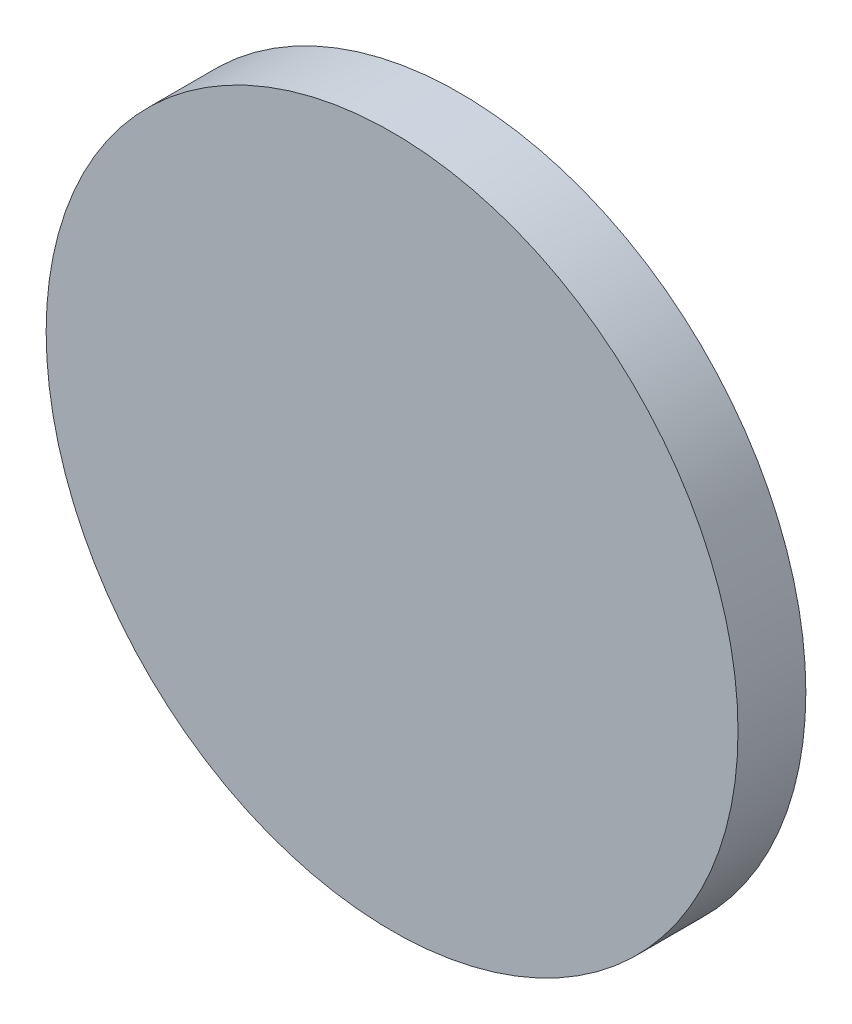
SolidWorks part; units mm, degrees
material "glass"
ref_plane "Front Plane" through (0, 0, 0) normal (0, 0, 1) x (1, 0, 0)
ref_plane "Top Plane" through (0, 0, 0) normal (0, 1, 0) x (1, 0, 0)
ref_plane "Right Plane" through (0, 0, 0) normal (1, 0, 0) x (0, 0, -1)
sketch "Sketch1" plane through (0, 0, 0) normal (0, 0, 1) x (1, 0, 0)
  circle A0 centre (0, 0) radius 12.75
  dimension "D1" = 25.5
extrude "Boss-Extrude1" add sketch "Sketch1" along normal blind 2.5
